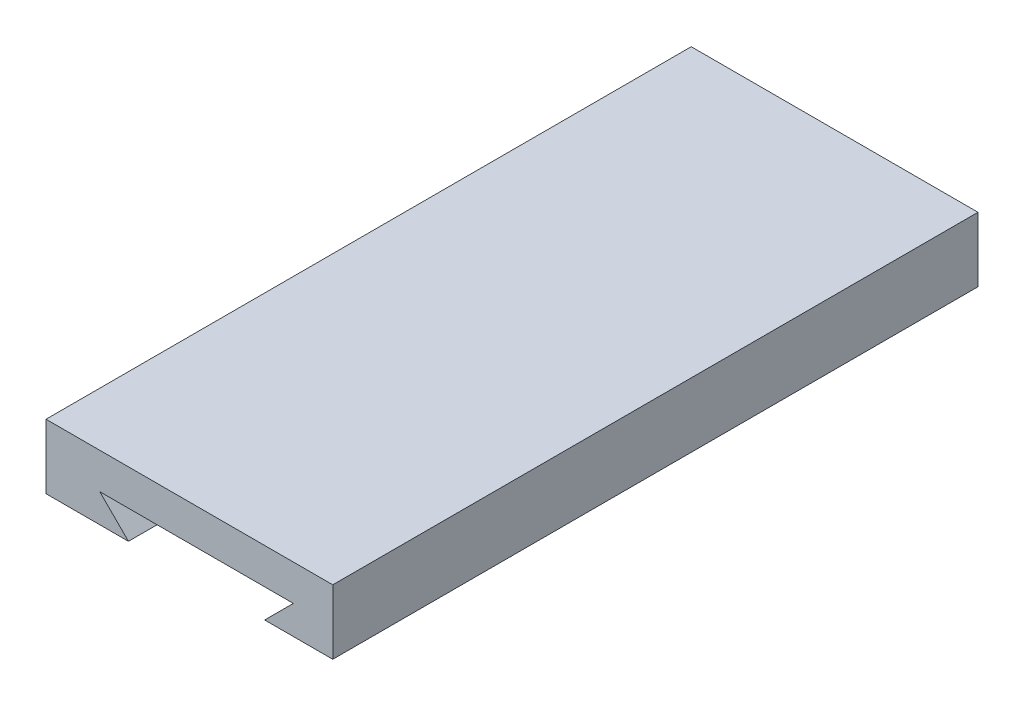
SolidWorks part; units mm, degrees
ref_plane "Front Plane" through (0, 0, 0) normal (0, 0, 1) x (1, 0, 0)
ref_plane "Top Plane" through (0, 0, 0) normal (0, 1, 0) x (1, 0, 0)
ref_plane "Right Plane" through (0, 0, 0) normal (1, 0, 0) x (0, 0, -1)
sketch "Sketch1" plane through (0, 0, 0) normal (0, 0, 1) x (1, 0, 0)
  line L1 (-51.0211, 23.825) -> (28.9789, 23.825)
  line L2 (-51.0211, 23.825) -> (-51.0211, 5.825)
  line L3 (-51.0211, 5.825) -> (28.9789, 5.825)
  line L4 (28.9789, 23.825) -> (28.9789, 5.825)
  dimension "D1" = 80
  dimension "D2" = 18
extrude "Boss-Extrude1" add sketch "Sketch1" along normal blind 180
sketch "Sketch2" plane through (0, 0, 180) normal (0, 0, 1) x (1, 0, 0)
  line L0 (-28.0211, 5.825) -> (-36.0211, 13.825)
  line L1 (-51.0211, 5.825) -> (28.9789, 5.825) construction
  line L2 (-36.0211, 13.825) -> (17.9789, 13.825)
  line L3 (17.9789, 13.825) -> (9.9789, 5.825)
  line L4 (-28.0211, 5.825) -> (9.9789, 5.825)
  line L6 (28.9789, 5.825) -> (28.9789, 23.825) construction
  dimension "D1" = 45
  dimension "D2" = 45
  dimension "D3" = 54
  dimension "D4" = 11
  dimension "D5" = 8
extrude "Cut-Extrude1" cut sketch "Sketch2" against normal blind 180 and the other way through all
